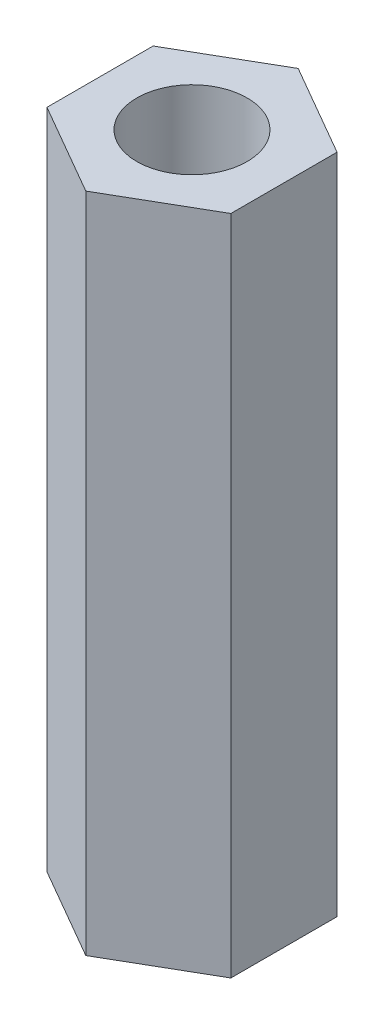
SolidWorks part; units mm, degrees
ref_plane "前基準面" through (0, 0, 0) normal (0, 0, 1) x (1, 0, 0)
ref_plane "上基準面" through (0, 0, 0) normal (0, 1, 0) x (1, 0, 0)
ref_plane "右基準面" through (0, 0, 0) normal (1, 0, 0) x (0, 0, -1)
sketch "草圖1" plane through (0, 0, 0) normal (0, 1, 0) x (1, 0, 0)
  line L0 (0, -5.1664) -> (0, 5.1664) construction
  line L1 (0, 2.8868) -> (-2.5, 1.4434)
  line L2 (-2.5, 1.4434) -> (-2.5, -1.4434)
  line L3 (-2.5, -1.4434) -> (0, -2.8868)
  line L4 (0, -2.8868) -> (2.5, -1.4434)
  line L5 (2.5, -1.4434) -> (2.5, 1.4434)
  line L6 (2.5, 1.4434) -> (0, 2.8868)
  circle A0 centre (0, 0) radius 1.5
  circle A1 centre (0, 0) radius 2.5 construction
  point P16 (0, 0)
  dimension "D1" = 3
  dimension "D2" = 5
extrude "填料-伸長1" add sketch "草圖1" along normal blind 18
